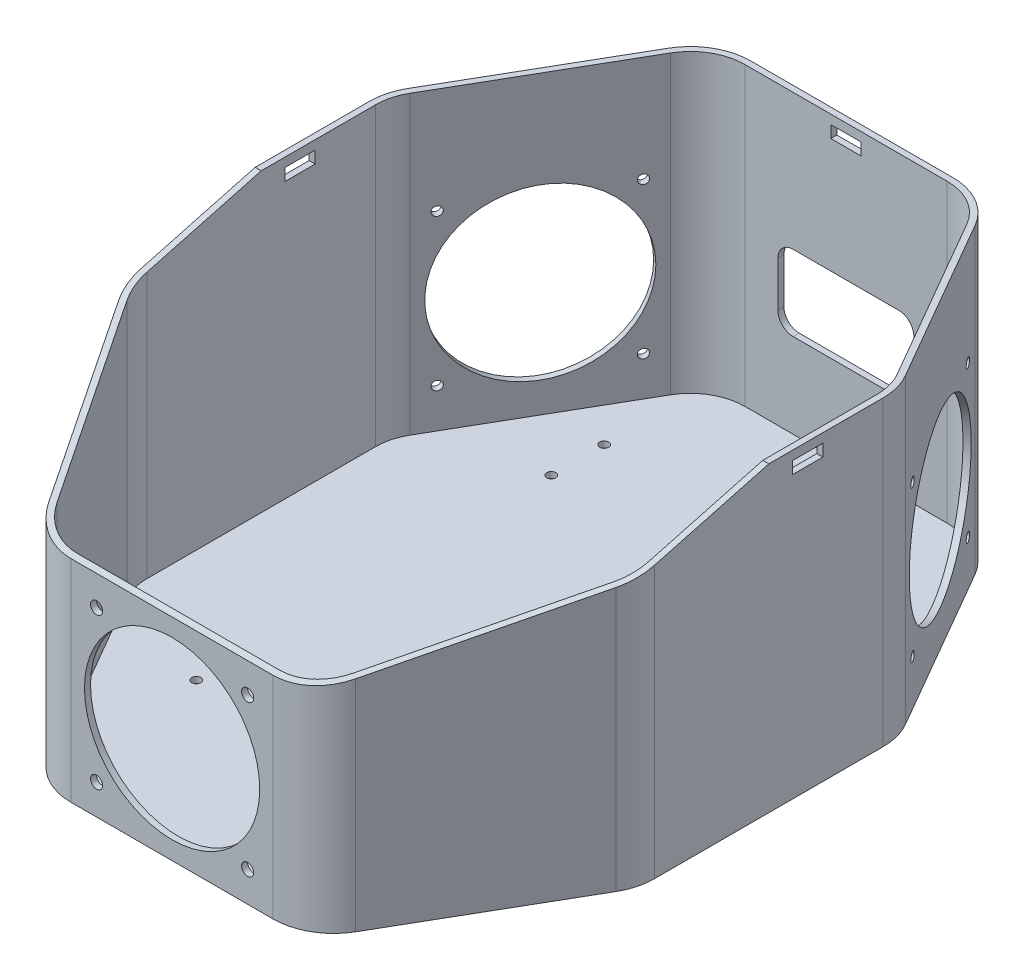
SolidWorks part; units mm, degrees
ref_plane "Alzado" through (0, 0, 0) normal (0, 0, 1) x (1, 0, 0)
ref_plane "Planta" through (0, 0, 0) normal (0, 1, 0) x (1, 0, 0)
ref_plane "Vista lateral" through (0, 0, 0) normal (1, 0, 0) x (0, 0, -1)
sketch "Croquis1" plane through (0, 0, 0) normal (0, 1, 0) x (1, 0, 0)
  line L0 (-82.3205, 47.859) -> (-50.7735, 102.5)
  line L1 (-33.453, 112.5) -> (33.453, 112.5)
  line L2 (-85, 37.859) -> (-85, -37.859)
  line L3 (-65, -112.5) -> (65, -112.5) construction
  line L4 (85, 37.859) -> (85, -37.859)
  line L5 (-85, 112.5) -> (85, -112.5) construction
  line L6 (-85, -112.5) -> (85, 112.5) construction
  line L7 (0, 0) -> (0, 35.0425) construction
  line L8 (82.3205, 47.859) -> (50.7735, 102.5)
  line L9 (-85, 112.5) -> (-45, 112.5) construction
  line L10 (0, 0) -> (34.8014, 0) construction
  line L11 (82.3205, -47.859) -> (50.7735, -102.5)
  line L12 (-33.453, -112.5) -> (33.453, -112.5)
  line L13 (-82.3205, -47.859) -> (-50.7735, -102.5)
  arc A0 (-85, -92.5) -> (-65, -112.5) centre (-65, -92.5) ccw construction
  arc A1 (65, -112.5) -> (85, -92.5) centre (65, -92.5) ccw construction
  arc A2 (82.3205, 47.859) -> (85, 37.859) centre (65, 37.859) cw
  arc A3 (50.7735, 102.5) -> (33.453, 112.5) centre (33.453, 92.5) ccw
  arc A4 (-50.7735, 102.5) -> (-33.453, 112.5) centre (-33.453, 92.5) cw
  arc A5 (-82.3205, 47.859) -> (-85, 37.859) centre (-65, 37.859) ccw
  arc A6 (82.3205, -47.859) -> (85, -37.859) centre (65, -37.859) ccw
  arc A7 (50.7735, -102.5) -> (33.453, -112.5) centre (33.453, -92.5) cw
  arc A8 (-50.7735, -102.5) -> (-33.453, -112.5) centre (-33.453, -92.5) ccw
  arc A9 (-82.3205, -47.859) -> (-85, -37.859) centre (-65, -37.859) cw
  point P0 (0, 0)
  point P21 (85, 43.218)
  point P24 (45, 112.5)
  point P30 (-85, 43.218)
  dimension "D5" = 20
  dimension "D1" = 30
  dimension "D2" = 80
  dimension "D3" = 225
  dimension "D4" = 170
extrude "Saliente-Extruir1" add sketch "Croquis1" along normal blind 100
shell "Vaciado2" thickness 2
sketch "Croquis2" plane through (0, 0, 0) normal (0, 1, 0) x (1, 0, 0)
  line L0 (0, 58.75) -> (0, -58.75) construction
  line L1 (-45.75, 58.75) -> (45.75, 58.75) construction
  line L2 (-45.75, -58.75) -> (45.75, -58.75) construction
  line L3 (-45.75, 58.75) -> (-45.75, 76.25) construction
  line L4 (45.75, -58.75) -> (45.75, -76.25) construction
  line L5 (-45.75, 76.25) -> (-40.1485, 76.25) construction
  line L6 (83, -37.859) -> (83, 37.859)
  line L7 (80.5885, 46.859) -> (49.0415, 101.5)
  line L8 (33.453, 110.5) -> (-33.453, 110.5)
  line L9 (-49.0415, 101.5) -> (-80.5885, 46.859)
  line L10 (-83, 37.859) -> (-83, -37.859)
  line L11 (-80.5885, -46.859) -> (-49.0415, -101.5)
  line L12 (83, -37.859) -> (83, 37.859) construction
  line L13 (80.5885, 46.859) -> (49.0415, 101.5) construction
  line L14 (33.453, 110.5) -> (-33.453, 110.5) construction
  line L15 (-49.0415, 101.5) -> (-80.5885, 46.859) construction
  line L16 (-83, 37.859) -> (-83, -37.859) construction
  line L18 (-35.75, 76.25) -> (25.75, 76.25) construction
  line L19 (-35.75, 76.25) -> (-35.75, 48.75) construction
  line L20 (-35.75, 48.75) -> (25.75, 48.75) construction
  line L21 (25.75, 76.25) -> (25.75, 48.75) construction
  line L22 (-35.75, 76.25) -> (25.75, 48.75) construction
  line L23 (-35.75, 48.75) -> (25.75, 76.25) construction
  line L24 (45.75, -76.25) -> (34.6741, -76.25) construction
  line L25 (-25.75, -76.25) -> (35.75, -76.25) construction
  line L26 (-25.75, -76.25) -> (-25.75, -13.75) construction
  line L27 (-25.75, -13.75) -> (35.75, -13.75) construction
  line L28 (35.75, -76.25) -> (35.75, -13.75) construction
  line L29 (-25.75, -76.25) -> (35.75, -13.75) construction
  line L30 (-25.75, -13.75) -> (35.75, -76.25) construction
  line L37 (-80.5885, -46.859) -> (-49.0415, -101.5) construction
  line L42 (-33.453, -110.5) -> (33.453, -110.5)
  line L44 (-33.453, -110.5) -> (33.453, -110.5) construction
  line L45 (49.0415, -101.5) -> (80.5885, -46.859)
  line L46 (49.0415, -101.5) -> (80.5885, -46.859) construction
  circle A0 centre (-45.75, 76.25) radius 1.5
  circle A1 centre (-45.75, 58.75) radius 1.5
  circle A2 centre (45.75, 58.75) radius 1.5
  circle A3 centre (-45.75, -58.75) radius 1.5
  circle A4 centre (45.75, -58.75) radius 1.5
  circle A5 centre (45.75, -76.25) radius 1.5
  arc A12 (-83, -37.859) -> (-80.5885, -46.859) centre (-65, -37.859) ccw
  arc A14 (-83, -37.859) -> (-80.5885, -46.859) centre (-65, -37.859) ccw construction
  arc A16 (83, 37.859) -> (80.5885, 46.859) centre (65, 37.859) ccw
  arc A17 (83, 37.859) -> (80.5885, 46.859) centre (65, 37.859) ccw construction
  arc A18 (49.0415, 101.5) -> (33.453, 110.5) centre (33.453, 92.5) ccw
  arc A19 (49.0415, 101.5) -> (33.453, 110.5) centre (33.453, 92.5) ccw construction
  arc A20 (-33.453, 110.5) -> (-49.0415, 101.5) centre (-33.453, 92.5) ccw
  arc A21 (-33.453, 110.5) -> (-49.0415, 101.5) centre (-33.453, 92.5) ccw construction
  arc A22 (-80.5885, 46.859) -> (-83, 37.859) centre (-65, 37.859) ccw
  arc A23 (-80.5885, 46.859) -> (-83, 37.859) centre (-65, 37.859) ccw construction
  arc A24 (-49.0415, -101.5) -> (-33.453, -110.5) centre (-33.453, -92.5) ccw
  arc A25 (-49.0415, -101.5) -> (-33.453, -110.5) centre (-33.453, -92.5) ccw construction
  arc A30 (33.453, -110.5) -> (49.0415, -101.5) centre (33.453, -92.5) ccw
  arc A31 (33.453, -110.5) -> (49.0415, -101.5) centre (33.453, -92.5) ccw construction
  arc A32 (80.5885, -46.859) -> (83, -37.859) centre (65, -37.859) ccw
  arc A33 (80.5885, -46.859) -> (83, -37.859) centre (65, -37.859) ccw construction
  point P21 (-5, 62.5)
  point P26 (5, -45)
  dimension "D5" = 3
  dimension "D2" = 91.5
  dimension "D3" = 17.5
  dimension "D4" = 17.5
  dimension "D6" = 10
  dimension "D7" = 20
  dimension "D8" = 10
  dimension "D9" = 20
  dimension "D10" = 10
  dimension "D11" = 45
  dimension "D12" = 117.5
  dimension "D1" = 0
extrude "Cortar-Extruir1" cut sketch "Croquis2" along normal through all both and the other way through all
sketch "Croquis3" plane through (0, 0, 0) normal (1, 0, 0) x (0, 0, -1)
  line L0 (27, 65) -> (27, 80) construction
  line L1 (-25, 65) -> (25, 65) construction
  line L2 (-25, 65) -> (-25, 15) construction
  line L3 (-25, 15) -> (25, 15) construction
  line L4 (25, 65) -> (25, 15) construction
  line L5 (-25, 65) -> (25, 15) construction
  line L6 (-25, 15) -> (25, 65) construction
  line L10 (-37.859, 0) -> (37.859, 0)
  line L11 (37.859, 0) -> (37.859, 100)
  line L12 (37.859, 100) -> (-37.859, 100)
  line L13 (-37.859, 100) -> (-37.859, 0)
  line L14 (-37.859, 0) -> (37.859, 0) construction
  line L15 (37.859, 0) -> (37.859, 100) construction
  line L16 (37.859, 100) -> (-37.859, 100) construction
  line L19 (7.5, 95.5) -> (27, 95.5) construction
  line L21 (7.5, 95.5) -> (7.5, 80) construction
  line L22 (7.5, 80) -> (27, 80) construction
  line L23 (27, 95.5) -> (27, 80) construction
  line L24 (7.5, 95.5) -> (27, 80) construction
  line L25 (7.5, 80) -> (27, 95.5) construction
  line L26 (-37.859, 100) -> (37.859, 0) construction
  line L27 (0, 40) -> (0, 50) construction
  line L30 (-37.859, 100) -> (-37.859, 0) construction
  circle A0 centre (-25, 15) radius 2
  circle A1 centre (25, 15) radius 2
  circle A2 centre (25, 65) radius 2
  circle A3 centre (-25, 65) radius 2
  circle A4 centre (0, 40) radius 29
  point P0 (0, 40)
  point P13 (17.25, 87.75)
  dimension "D6" = 4
  dimension "D10" = 58
  dimension "D1" = 50
  dimension "D2" = 50
  dimension "D4" = 15
  dimension "D7" = 19.5
  dimension "D8" = 15.5
  dimension "D9" = 15
  dimension "D3" = 0
sketch "Croquis7" plane through (0, 0, 0) normal (0, 0, 1) x (1, 0, 0)
  line L1 (25, 60) -> (-25, 60) construction
  line L2 (25, 60) -> (25, 10) construction
  line L3 (25, 10) -> (-25, 10) construction
  line L4 (-25, 60) -> (-25, 10) construction
  line L5 (25, 60) -> (-25, 10) construction
  line L6 (25, 10) -> (-25, 60) construction
  circle A0 centre (25, 60) radius 2
  circle A1 centre (-25, 60) radius 2
  circle A2 centre (-25, 10) radius 2
  circle A3 centre (25, 10) radius 2
  circle A4 centre (0, 35) radius 29
  point P0 (0, 35)
  dimension "D1" = 4
  dimension "D5" = 58
  dimension "D2" = 50
  dimension "D3" = 50
  dimension "D4" = 10
ref_plane "Plano1" through (0, 0, 0) normal (0.866, 0, -0.5) x (-0.5, 0, -0.866)
sketch "Croquis8" plane through (0, 0, 0) normal (0.866, 0, -0.5) x (-0.5, 0, -0.866)
  line L1 (6.8338, 15) -> (56.8338, 15) construction
  line L2 (6.8338, 15) -> (6.8338, 65) construction
  line L3 (6.8338, 65) -> (56.8338, 65) construction
  line L4 (0.2868, 0) -> (63.3809, 0)
  line L5 (63.3809, 0) -> (63.3809, 100)
  line L6 (63.3809, 100) -> (0.2868, 100)
  line L7 (0.2868, 100) -> (0.2868, 0)
  line L8 (0.2868, 0) -> (63.3809, 0) construction
  line L9 (63.3809, 0) -> (63.3809, 100) construction
  line L10 (63.3809, 100) -> (0.2868, 100) construction
  line L11 (0.2868, 100) -> (0.2868, 0) construction
  line L12 (56.8338, 15) -> (56.8338, 65) construction
  line L13 (6.8338, 15) -> (56.8338, 65) construction
  line L14 (6.8338, 65) -> (56.8338, 15) construction
  line L16 (31.8338, 40) -> (31.8338, 0) construction
  circle A0 centre (31.8338, 40) radius 28
  circle A1 centre (6.8338, 65) radius 1.5
  circle A2 centre (56.8338, 65) radius 1.5
  circle A3 centre (6.8338, 15) radius 1.5
  circle A4 centre (56.8338, 15) radius 1.5
  dimension "D2" = 3
  dimension "D6" = 56
  dimension "D3" = 50
  dimension "D4" = 50
  dimension "D5" = 15
  dimension "D1" = 0
extrude "Cortar-Extruir6" cut sketch "Croquis8" along normal through all
mirror "Simetría1" about plane through (0, 0, 0) normal (1, 0, 0) of "Cortar-Extruir6"
mirror "Simetría2" [suppressed] about plane through (0, 0, 0) normal (0, 0, 1)
sketch "Croquis9" plane through (0, 0, 0) normal (0, 0, 1) x (1, 0, 0)
  line L0 (0, 42.5) -> (0, 0) construction
  line L1 (33.453, 0) -> (-33.453, 0) construction
  line L2 (17.5, 55) -> (-17.5, 55)
  line L3 (22.5, 50) -> (22.5, 35)
  line L4 (17.5, 30) -> (-17.5, 30)
  line L5 (-22.5, 50) -> (-22.5, 35)
  line L6 (22.5, 55) -> (-22.5, 30) construction
  line L7 (22.5, 30) -> (-22.5, 55) construction
  arc A1 (-17.5, 55) -> (-22.5, 50) centre (-17.5, 50) ccw
  arc A2 (-17.5, 30) -> (-22.5, 35) centre (-17.5, 35) cw
  arc A3 (22.5, 35) -> (17.5, 30) centre (17.5, 35) cw
  arc A4 (17.5, 55) -> (22.5, 50) centre (17.5, 50) cw
  dimension "D1" = 5
  dimension "D2" = 30
  dimension "D3" = 25
  dimension "D4" = 45
extrude "Cortar-Extruir7" cut sketch "Croquis9" against normal through all
sketch "Croquis10" plane through (0, 0, 0) normal (1, 0, 0) x (0, 0, -1)
  line L0 (0, 0) -> (0, 100) construction
  line L1 (-37.859, 100) -> (37.859, 100) construction
  line L2 (0, 100) -> (-148.8276, 60.1218)
  line L3 (-102.5, 100) -> (-47.859, 100) construction
  line L4 (-148.8276, 60.1218) -> (-148.8276, 114.2872)
  line L5 (-148.8276, 114.2872) -> (0, 114.2872)
  line L6 (0, 114.2872) -> (0, 100)
  dimension "D1" = 15
extrude "Cortar-Extruir8" cut sketch "Croquis10" against normal through all both and the other way through all
sketch "Croquis11" plane through (0, 0, 0) normal (0, 0, 1) x (1, 0, 0)
  circle A1 centre (0, 35) radius 29
  circle A2 centre (0, 35) radius 29
  circle A3 centre (25, 10) radius 2
  circle A4 centre (25, 10) radius 2
  circle A5 centre (-25, 10) radius 2
  circle A6 centre (-25, 10) radius 2
  circle A7 centre (-25, 60) radius 2
  circle A8 centre (-25, 60) radius 2
  circle A9 centre (25, 60) radius 2
  circle A10 centre (25, 60) radius 2
  dimension "D1" = 0
  dimension "D2" = 0
  dimension "D3" = 0
  dimension "D4" = 0
  dimension "D5" = 0
extrude "Cortar-Extruir9" cut sketch "Croquis11" along normal through all
sketch "Croquis12" plane through (0, 0, 0) normal (1, 0, 0) x (0, 0, -1)
  line L0 (0, -16.0558) -> (0, 131.6545)
sketch "Croquis13" plane through (0, 0, 0) normal (0, 0, 1) x (1, 0, 0)
  line L0 (0, 95) -> (0, 100) construction
  line L1 (5, 97) -> (-5, 97)
  line L2 (5, 97) -> (5, 93)
  line L3 (5, 93) -> (-5, 93)
  line L4 (-33.453, 0) -> (33.453, 0)
  line L5 (-33.453, 100) -> (-33.453, 0)
  line L6 (33.453, 100) -> (-33.453, 100)
  line L7 (33.453, 0) -> (33.453, 100)
  line L8 (-33.453, 0) -> (33.453, 0) construction
  line L9 (-33.453, 100) -> (-33.453, 0) construction
  line L10 (33.453, 100) -> (-33.453, 100) construction
  line L11 (33.453, 0) -> (33.453, 100) construction
  line L12 (-5, 97) -> (-5, 93)
  line L13 (5, 97) -> (-5, 93) construction
  line L14 (5, 93) -> (-5, 97) construction
  point P2 (0, 95)
  dimension "D2" = 10
  dimension "D3" = 4
  dimension "D4" = 3
  dimension "D1" = 0
extrude "Cortar-Extruir10" cut sketch "Croquis13" against normal through all
sketch "Croquis14" plane through (0, 0, 0) normal (1, 0, 0) x (0, 0, -1)
  line L1 (7.859, 97) -> (17.859, 97)
  line L2 (7.859, 97) -> (7.859, 93)
  line L3 (7.859, 93) -> (17.859, 93)
  line L4 (17.859, 97) -> (17.859, 93)
  line L5 (37.859, 100) -> (0, 100)
  line L6 (0, 100) -> (-37.859, 89.8557)
  line L7 (-37.859, 89.8557) -> (-37.859, 0)
  line L8 (-37.859, 0) -> (37.859, 0)
  line L9 (37.859, 0) -> (37.859, 100)
  line L10 (37.859, 100) -> (0, 100) construction
  line L11 (0, 100) -> (-37.859, 89.8557) construction
  line L12 (-37.859, 89.8557) -> (-37.859, 0) construction
  line L13 (-37.859, 0) -> (37.859, 0) construction
  line L14 (37.859, 0) -> (37.859, 100) construction
  line L15 (7.859, 97) -> (17.859, 93) construction
  line L16 (7.859, 93) -> (17.859, 97) construction
  point P2 (12.859, 95)
  dimension "D2" = 10
  dimension "D3" = 4
  dimension "D4" = 3
  dimension "D5" = 20
  dimension "D1" = 0
extrude "Cortar-Extruir11" cut sketch "Croquis14" against normal through all both and the other way through all
